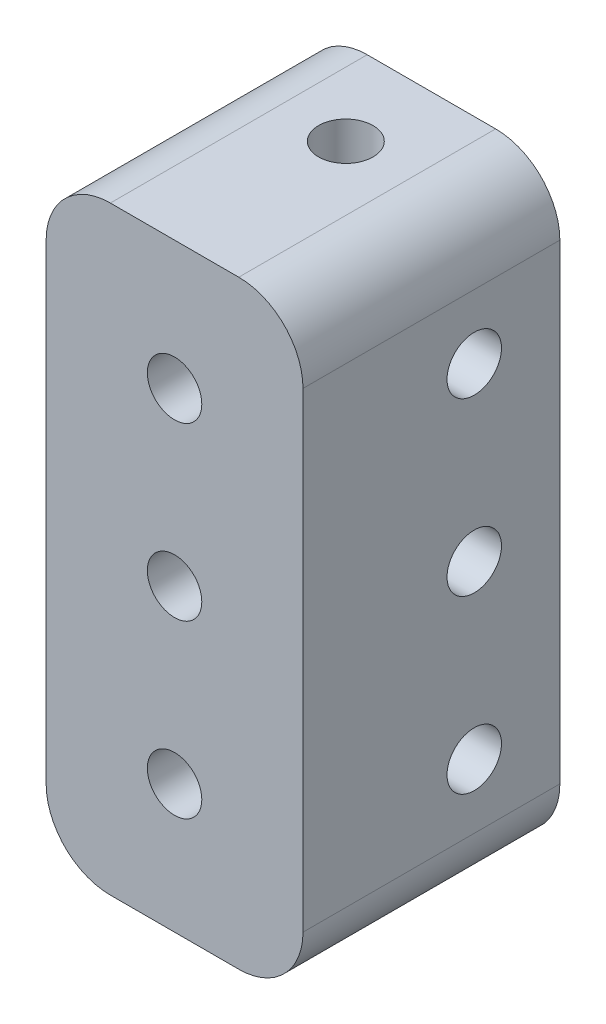
SolidWorks part; units mm, degrees
ref_plane "Front Plane" through (0, 0, 0) normal (0, 0, 1) x (1, 0, 0)
ref_plane "Top Plane" through (0, 0, 0) normal (0, 1, 0) x (1, 0, 0)
ref_plane "Right Plane" through (0, 0, 0) normal (1, 0, 0) x (0, 0, -1)
sketch "Sketch1" plane through (0, 0, 0) normal (0, 0, 1) x (1, 0, 0)
  line L0 (-9.525, 22.225) -> (-9.525, -22.225) construction
  line L1 (-9.525, 22.225) -> (9.525, 22.225) construction
  line L2 (-9.525, 0) -> (0, 0) construction
  line L3 (0, 0) -> (0, 22.225) construction
  dimension "Thickness" = 19.05
  dimension "Width" = 44.45
ref_plane "Plane1" through (-9.525, 22.225, 0) normal (0, -1, 0) x (-1, 0, 0)
sketch "Sketch2" plane through (-9.525, 22.225, 0) normal (0, 1, 0) x (1, 0, 0)
  line L0 (9.525, -457.2) -> (9.525, 457.2) construction
  point P2 (9.525, -390.525)
  point P3 (9.525, 390.525)
  dimension "Length" = 914.4
  dimension "D1" = 66.675
  dimension "D2" = 66.675
sketch "Sketch3" plane through (0, 0, 0) normal (0, 0, 1) x (1, 0, 0)
  line L1 (-9.525, -22.225) -> (9.525, -22.225)
  line L2 (-9.525, -22.225) -> (-9.525, 22.225)
  line L3 (-9.525, 22.225) -> (9.525, 22.225)
  line L4 (9.525, -22.225) -> (9.525, 22.225)
  line L5 (0, 22.225) -> (0, -22.225) construction
  line L6 (-9.525, 0) -> (9.525, 0) construction
  line L7 (-9.525, 0) -> (0, 0) construction
extrude "Boss-Extrude1" add sketch "Sketch3" along normal up to vertex (457.2 mm away) and the other way up to vertex (457.2 mm away) up to point (0, 22.225, 457.2) other way up to point (0, 22.225, -457.2)
fillet "Fillet1" radius 4.7625 4 edges at (9.525, -22.225, 0) (-9.525, -22.225, 0) (9.525, 22.225, 0) (-9.525, 22.225, 0)
sketch "Sketch4" plane through (9.525, 0, 0) normal (1, 0, 0) x (0, 0, -1)
  line L0 (457.2, -17.4625) -> (457.2, 17.4625) construction
  line L1 (-9.525, 22.225) -> (-457.2, 22.225)
  line L2 (-9.525, 22.225) -> (-9.525, -22.225)
  line L3 (-9.525, -22.225) -> (-457.2, -22.225)
  line L4 (-457.2, 22.225) -> (-457.2, -22.225)
  line L5 (9.525, 22.225) -> (457.2, 22.225)
  line L6 (9.525, 22.225) -> (9.525, -22.225)
  line L7 (9.525, -22.225) -> (457.2, -22.225)
  line L8 (457.2, 22.225) -> (457.2, -22.225)
  line L9 (-457.2, 22.225) -> (457.2, 22.225) construction
  line L10 (457.2, -22.225) -> (-457.2, -22.225) construction
  line L11 (-457.2, -17.4625) -> (-457.2, 17.4625) construction
  line L12 (-9.525, 0) -> (9.525, 0) construction
  point P20 (0, 0)
  dimension "D1" = 19.05
extrude "Cut-Extrude1" cut sketch "Sketch4" against normal through all
sketch "Sketch7" plane through (9.525, 0, 0) normal (1, 0, 0) x (0, 0, -1)
  line L0 (3.175, 12.7) -> (3.175, 0) construction
  line L1 (3.175, 0) -> (3.175, -12.7) construction
  line L3 (-9.525, -17.4625) -> (-9.525, 17.4625) construction
  line L5 (0, 0) -> (3.175, 0) construction
  point P18 (3.175, 12.7)
  point P20 (3.175, 0)
  point P22 (3.175, -12.7)
  dimension "D1" = 12.7
  dimension "D2" = 12.7
hole_wizard "#10-32 Tapped Hole1" positions "Sketch7" profile "Sketch6" tap size "#10-32" standard "ANSI Inch"
cosmetic thread "Hole Thread1" parameters "D1"=9.652, "D2"=4.826
cosmetic thread "Hole Thread2" parameters "D1"=9.652, "D2"=4.826
cosmetic thread "Hole Thread3" parameters "D1"=9.652, "D2"=4.826
sketch "Sketch6" plane through (9.525, 12.7, -3.175) normal (0, 1, 0) x (0, 0, -1)
  line L0 (0, 0) -> (0, 10.7383)
  line L1 (0, 10.7383) -> (2.0193, 9.525)
  line L2 (2.0193, 9.525) -> (2.0193, 0)
  line L5 (2.0193, 0) -> (0, 0)
  line L10 (0, 10.7383) -> (-2.0193, 9.525) construction
  line L11 (0, -6.35) -> (0, 107.95) construction
  dimension "Tap Drill Dia." = 4.0386
  dimension "Tap Drill Depth" = 9.525
  dimension "Drill Angle" = 118
sketch "Sketch10" plane through (0, 0, 9.525) normal (0, 0, 1) x (1, 0, 0)
  line L0 (0, 12.7) -> (0, 0) construction
  line L1 (0, 0) -> (0, -12.7) construction
  point P5 (0, 0)
  point P8 (0, 12.7)
  point P10 (0, -12.7)
  dimension "D1" = 12.7
hole_wizard "#10-32 Tapped Hole2" positions "Sketch10" profile "Sketch9" tap size "#10-32" standard "ANSI Inch"
cosmetic thread "Hole Thread4" parameters "D1"=9.652, "D2"=4.826
cosmetic thread "Hole Thread5" parameters "D1"=9.652, "D2"=4.826
cosmetic thread "Hole Thread6" parameters "D1"=9.652, "D2"=4.826
sketch "Sketch9" plane through (0, 0, 9.525) normal (1, 0, 0) x (0, -1, 0)
  line L0 (0, 0) -> (0, 10.7383)
  line L1 (0, 10.7383) -> (2.0193, 9.525)
  line L2 (2.0193, 9.525) -> (2.0193, 0)
  line L5 (2.0193, 0) -> (0, 0)
  line L10 (0, 10.7383) -> (-2.0193, 9.525) construction
  line L11 (0, -6.35) -> (0, 107.95) construction
  dimension "Tap Drill Dia." = 4.0386
  dimension "Tap Drill Depth" = 9.525
  dimension "Drill Angle" = 118
sketch "Sketch13" plane through (0, 22.225, 0) normal (0, 1, 0) x (1, 0, 0)
  line L0 (0, 0) -> (0, 3.175) construction
  line L2 (-4.7625, -9.525) -> (4.7625, -9.525) construction
  point P6 (0, 3.175)
  dimension "D1" = 12.7
hole_wizard "#10-32 Tapped Hole3" positions "Sketch13" profile "Sketch12" tap size "#10-32" standard "ANSI Inch"
sketch "Sketch12" plane through (0, 22.225, -3.175) normal (1, 0, 0) x (0, 0, 1)
  line L0 (0, 0) -> (0, 10.7383)
  line L1 (0, 10.7383) -> (2.0193, 9.525)
  line L2 (2.0193, 9.525) -> (2.0193, 0)
  line L5 (2.0193, 0) -> (0, 0)
  line L10 (0, 10.7383) -> (-2.0193, 9.525) construction
  line L11 (0, -6.35) -> (0, 107.95) construction
  dimension "Tap Drill Dia." = 4.0386
  dimension "Tap Drill Depth" = 9.525
  dimension "Drill Angle" = 118
cosmetic thread "Hole Thread7" parameters "D1"=9.652, "D2"=4.826
mirror "Mirror1" about plane through (0, 0, 0) normal (0, 1, 0) of "#10-32 Tapped Hole3"
mirror "Mirror2" about plane through (0, 0, 0) normal (1, 0, 0) of "#10-32 Tapped Hole1"
equation "\"D1@Sketch2\"=\"Width@Sketch1\"*1.5"
equation "\"D2@Sketch2\"=\"D1@Sketch2\""
equation "\"D1@Fillet1\"=\"Thickness@Sketch1\"/4"
